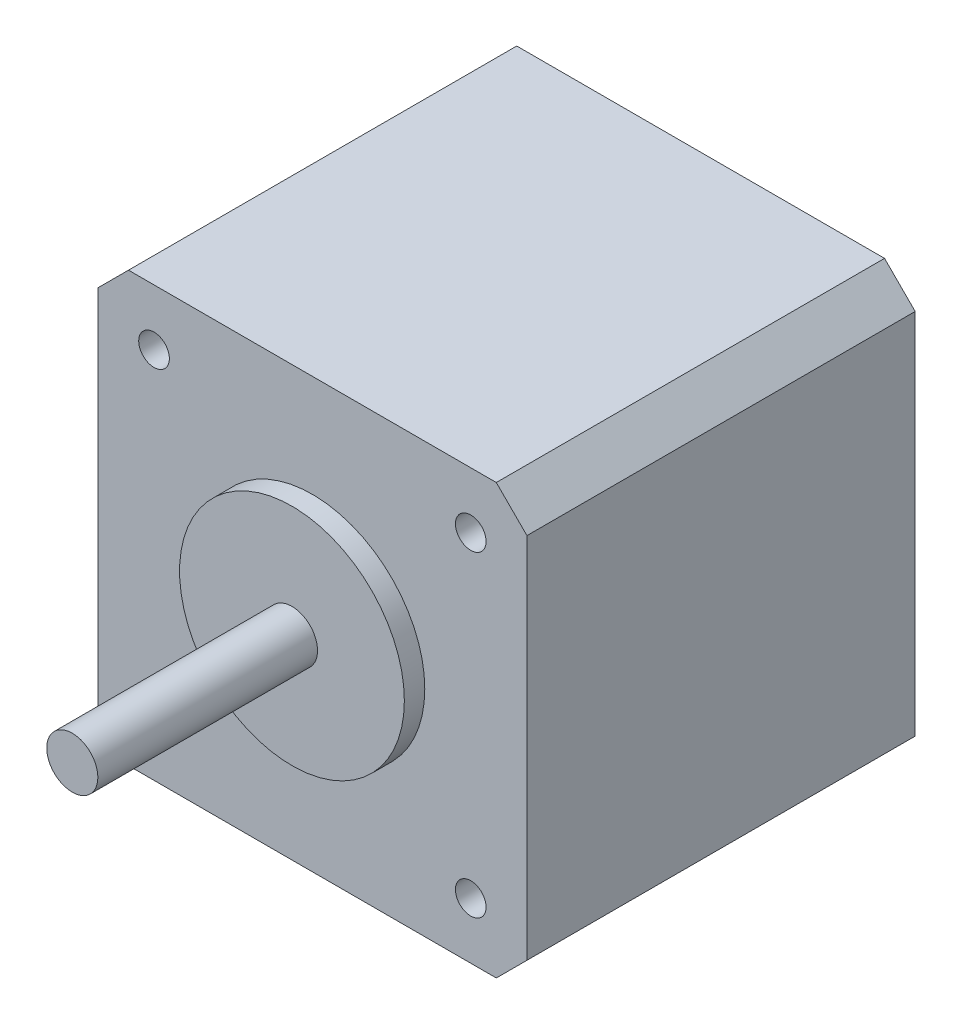
SolidWorks part; units mm, degrees
material "1060 Alloy"
ref_plane "Front Plane" through (0, 0, 0) normal (0, 0, 1) x (1, 0, 0)
ref_plane "Top Plane" through (0, 0, 0) normal (0, 1, 0) x (1, 0, 0)
ref_plane "Right Plane" through (0, 0, 0) normal (1, 0, 0) x (0, 0, -1)
sketch "Sketch1" plane through (0, 0, 0) normal (0, 0, 1) x (1, 0, 0)
  line L1 (-21, 21) -> (21, 21)
  line L2 (-21, 21) -> (-21, -21)
  line L3 (-21, -21) -> (21, -21)
  line L4 (21, 21) -> (21, -21)
  line L5 (-21, 21) -> (21, -21) construction
  line L6 (-21, -21) -> (21, 21) construction
  point P0 (0, 0)
  dimension "D1" = 42
  dimension "D2" = 42
extrude "Boss-Extrude1" add sketch "Sketch1" along normal blind 38
sketch "Sketch2" plane through (0, 0, 38) normal (0, 0, 1) x (1, 0, 0)
  circle A0 centre (0, 0) radius 11
  dimension "D1" = 22
extrude "Boss-Extrude2" add sketch "Sketch2" along normal blind 2
sketch "Sketch3" plane through (0, 0, 40) normal (0, 0, 1) x (1, 0, 0)
  circle A0 centre (0, 0) radius 2.5
  dimension "D1" = 5
extrude "Boss-Extrude3" add sketch "Sketch3" along normal blind 21.5
sketch "Sketch4" plane through (0, 0, 38) normal (0, 0, 1) x (1, 0, 0)
  line L0 (-15.5, 15.5) -> (15.5, -15.5) construction
  circle A0 centre (15.5, 15.5) radius 1.5
  circle A1 centre (15.5, -15.5) radius 1.5
  circle A2 centre (-15.5, -15.5) radius 1.5
  circle A3 centre (-15.5, 15.5) radius 1.5
  point P8 (0, 0)
  dimension "D3" = 3
  dimension "D4" = 3
  dimension "D5" = 3
  dimension "D6" = 3
  dimension "D1" = 31
  dimension "D2" = 31
extrude "Cut-Extrude1" cut sketch "Sketch4" against normal blind 4.5
chamfer "Chamfer1" distance 3 angle 45 4 edges at (-21, -21, 19) (-21, 21, 19) (21, -21, 19) (21, 21, 19)
